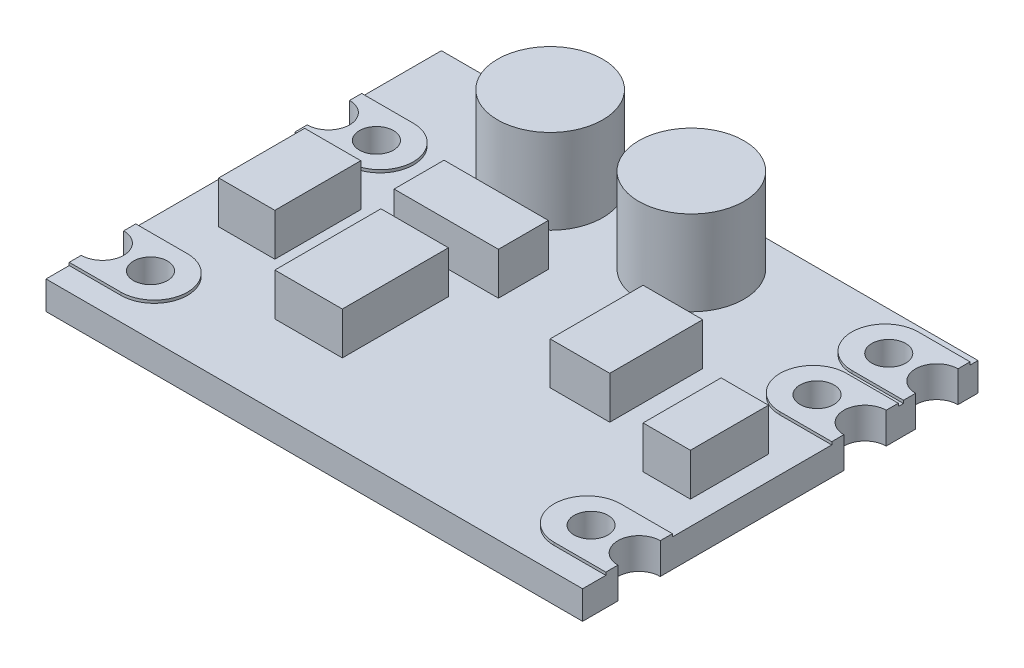
SolidWorks part; units mm, degrees
ref_plane "Спереди" through (0, 0, 0) normal (0, 0, 1) x (1, 0, 0)
ref_plane "Сверху" through (0, 0, 0) normal (0, 1, 0) x (1, 0, 0)
ref_plane "Справа" through (0, 0, 0) normal (1, 0, 0) x (0, 0, -1)
sketch "Эскиз1" plane through (0, 0, 0) normal (0, 1, 0) x (1, 0, 0)
  line L1 (-9.5, -7) -> (9.5, -7)
  line L2 (-9.5, -7) -> (-9.5, 7)
  line L3 (-9.5, 7) -> (9.5, 7)
  line L4 (9.5, -7) -> (9.5, 7)
  line L5 (-9.5, -7) -> (9.5, 7) construction
  line L6 (-9.5, 7) -> (9.5, -7) construction
  point P0 (0, 0)
  dimension "D1" = 19
  dimension "D2" = 14
extrude "Бобышка-Вытянуть1" add sketch "Эскиз1" along normal blind 1
sketch "Эскиз2" plane through (0, 1, 0) normal (0, 1, 0) x (1, 0, 0)
  line L0 (-9.5, 7) -> (-9.5, -7) construction
  line L1 (0, 7) -> (0, -7) construction
  line L2 (9.5, 7) -> (-9.5, 7) construction
  line L3 (-9.5, -7) -> (9.5, -7) construction
  circle A0 centre (-9.5, -5) radius 0.75
  circle A1 centre (-9.5, 3) radius 0.75
  circle A6 centre (9.5, 3) radius 0.75
  circle A7 centre (9.5, -5) radius 0.75
  circle A8 centre (9.5, 5.54) radius 0.75
  circle A10 centre (-7.8, 3) radius 0.6024
  circle A11 centre (-7.8, -5) radius 0.6024
  circle A12 centre (7.8, 3) radius 0.6024
  circle A13 centre (7.8, -5) radius 0.6024
  circle A14 centre (7.8, 5.54) radius 0.6024
  dimension "D1" = 1.5
  dimension "D6" = 8
  dimension "D7" = 2
  dimension "D4" = 1.2048
  dimension "D2" = 2
  dimension "D3" = 2
  dimension "D5" = 2
  dimension "D8" = 2
extrude "Вырез-Вытянуть1" cut sketch "Эскиз2" against normal through all
sketch "Эскиз3" plane through (0, 1, 0) normal (0, 1, 0) x (1, 0, 0)
  line L0 (-11.3319, -5) -> (-7.6681, -5) construction
  line L1 (-11.3319, -3.8218) -> (-7.6681, -3.8218)
  line L2 (-11.3319, -6.1782) -> (-7.6681, -6.1782)
  line L3 (-11.3319, 3) -> (-7.6681, 3) construction
  line L4 (-11.3319, 4.1782) -> (-7.6681, 4.1782)
  line L5 (-11.3319, 1.8218) -> (-7.6681, 1.8218)
  line L6 (0, 7) -> (0, 1.8218) construction
  line L7 (9.5, 7) -> (-9.5, 7) construction
  line L8 (11.3319, -5) -> (7.6681, -5) construction
  line L9 (11.3319, -3.8218) -> (7.6681, -3.8218)
  line L10 (11.3319, -6.1782) -> (7.6681, -6.1782)
  line L11 (11.3319, 3) -> (7.6681, 3) construction
  line L12 (11.3319, 4.1782) -> (7.6681, 4.1782)
  line L13 (11.3319, 1.8218) -> (7.6681, 1.8218)
  line L14 (11.3319, 5.54) -> (7.6681, 5.54) construction
  line L15 (11.3319, 6.7182) -> (7.6681, 6.7182)
  line L16 (11.3319, 4.3618) -> (7.6681, 4.3618)
  line L35 (9.5, 3.75) -> (9.5, 4.79)
  line L36 (9.5, 6.29) -> (9.5, 7)
  line L37 (9.5, 7) -> (-9.5, 7)
  line L38 (-9.5, 7) -> (-9.5, 3.75)
  line L39 (-9.5, 2.25) -> (-9.5, -4.25)
  line L40 (-9.5, -5.75) -> (-9.5, -7)
  line L41 (-9.5, -7) -> (9.5, -7)
  line L42 (9.5, -7) -> (9.5, -5.75)
  line L43 (9.5, -4.25) -> (9.5, 2.25)
  line L44 (9.5, 3.75) -> (9.5, 4.79)
  line L45 (9.5, 6.29) -> (9.5, 7)
  line L46 (9.5, 7) -> (-9.5, 7)
  line L47 (-9.5, 7) -> (-9.5, 3.75)
  line L48 (-9.5, 2.25) -> (-9.5, -4.25)
  line L49 (-9.5, -5.75) -> (-9.5, -7)
  line L50 (-9.5, -7) -> (9.5, -7)
  line L51 (9.5, -7) -> (9.5, -5.75)
  line L52 (9.5, -4.25) -> (9.5, 2.25)
  arc A0 (-11.3319, -3.8218) -> (-11.3319, -6.1782) centre (-11.3319, -5) ccw
  arc A1 (-7.6681, -6.1782) -> (-7.6681, -3.8218) centre (-7.6681, -5) ccw
  arc A2 (-11.3319, 4.1782) -> (-11.3319, 1.8218) centre (-11.3319, 3) ccw
  arc A3 (-7.6681, 1.8218) -> (-7.6681, 4.1782) centre (-7.6681, 3) ccw
  arc A4 (11.3319, -3.8218) -> (11.3319, -6.1782) centre (11.3319, -5) cw
  arc A5 (7.6681, -6.1782) -> (7.6681, -3.8218) centre (7.6681, -5) cw
  arc A6 (11.3319, 4.1782) -> (11.3319, 1.8218) centre (11.3319, 3) cw
  arc A7 (7.6681, 1.8218) -> (7.6681, 4.1782) centre (7.6681, 3) cw
  arc A8 (11.3319, 6.7182) -> (11.3319, 4.3618) centre (11.3319, 5.54) cw
  arc A9 (7.6681, 4.3618) -> (7.6681, 6.7182) centre (7.6681, 5.54) cw
  arc A20 (9.5, 3.75) -> (9.5, 2.25) centre (9.5, 3) ccw
  arc A21 (9.5, 6.29) -> (9.5, 4.79) centre (9.5, 5.54) ccw
  arc A22 (-9.5, 2.25) -> (-9.5, 3.75) centre (-9.5, 3) ccw
  arc A23 (-9.5, -5.75) -> (-9.5, -4.25) centre (-9.5, -5) ccw
  arc A24 (9.5, -4.25) -> (9.5, -5.75) centre (9.5, -5) ccw
  arc A25 (9.5, 3.75) -> (9.5, 2.25) centre (9.5, 3) ccw
  arc A26 (9.5, 6.29) -> (9.5, 4.79) centre (9.5, 5.54) ccw
  arc A27 (-9.5, 2.25) -> (-9.5, 3.75) centre (-9.5, 3) ccw
  arc A28 (-9.5, -5.75) -> (-9.5, -4.25) centre (-9.5, -5) ccw
  arc A29 (9.5, -4.25) -> (9.5, -5.75) centre (9.5, -5) ccw
  point P2 (-9.5, -5)
  point P12 (-9.5, 3)
  point P22 (9.5, -5)
  point P29 (9.5, 3)
  point P37 (9.5, 5.54)
  dimension "D3" = 0
  dimension "D1" = 2
  dimension "D2" = 2
sketch "Эскиз4" plane through (0, 1, 0) normal (0, 1, 0) x (1, 0, 0)
  circle A0 centre (-3.3839, 4.7344) radius 1.8627
  circle A1 centre (1.6161, 4.7344) radius 1.8627
  dimension "D1" = 2
extrude "Бобышка-Вытянуть2" add sketch "Эскиз4" along normal blind 3
extrude "Бобышка-Вытянуть3" add sketch "Эскиз3" along normal blind 0.1
sketch "Эскиз5" plane through (0, 1, 0) normal (0, 1, 0) x (1, 0, 0)
  line L1 (-4.2221, -0.4191) -> (-1.8317, -0.4191)
  line L2 (-4.2221, -0.4191) -> (-4.2221, -4.1756)
  line L3 (-4.2221, -4.1756) -> (-1.8317, -4.1756)
  line L4 (-1.8317, -0.4191) -> (-1.8317, -4.1756)
  line L9 (2.763, 1.8782) -> (4.8741, 1.8782)
  line L10 (2.763, 1.8782) -> (2.763, -1.4125)
  line L11 (2.763, -1.4125) -> (4.8741, -1.4125)
  line L12 (4.8741, 1.8782) -> (4.8741, -1.4125)
  line L13 (-8.0407, 0.6985) -> (-6.0538, 0.6985)
  line L14 (-8.0407, 0.6985) -> (-8.0407, -2.3439)
  line L15 (-8.0407, -2.3439) -> (-6.0538, -2.3439)
  line L16 (-6.0538, 0.6985) -> (-6.0538, -2.3439)
  line L17 (-4.5947, 2.1887) -> (-0.9003, 2.1887)
  line L18 (-4.5947, 2.1887) -> (-4.5947, 0.4191)
  line L19 (-4.5947, 0.4191) -> (-0.9003, 0.4191)
  line L20 (-0.9003, 2.1887) -> (-0.9003, 0.4191)
  line L21 (6.9851, 0.4191) -> (8.6616, 0.4191)
  line L22 (6.9851, 0.4191) -> (6.9851, -2.3439)
  line L23 (6.9851, -2.3439) -> (8.6616, -2.3439)
  line L24 (8.6616, 0.4191) -> (8.6616, -2.3439)
extrude "Бобышка-Вытянуть4" add sketch "Эскиз5" along normal blind 1.5
